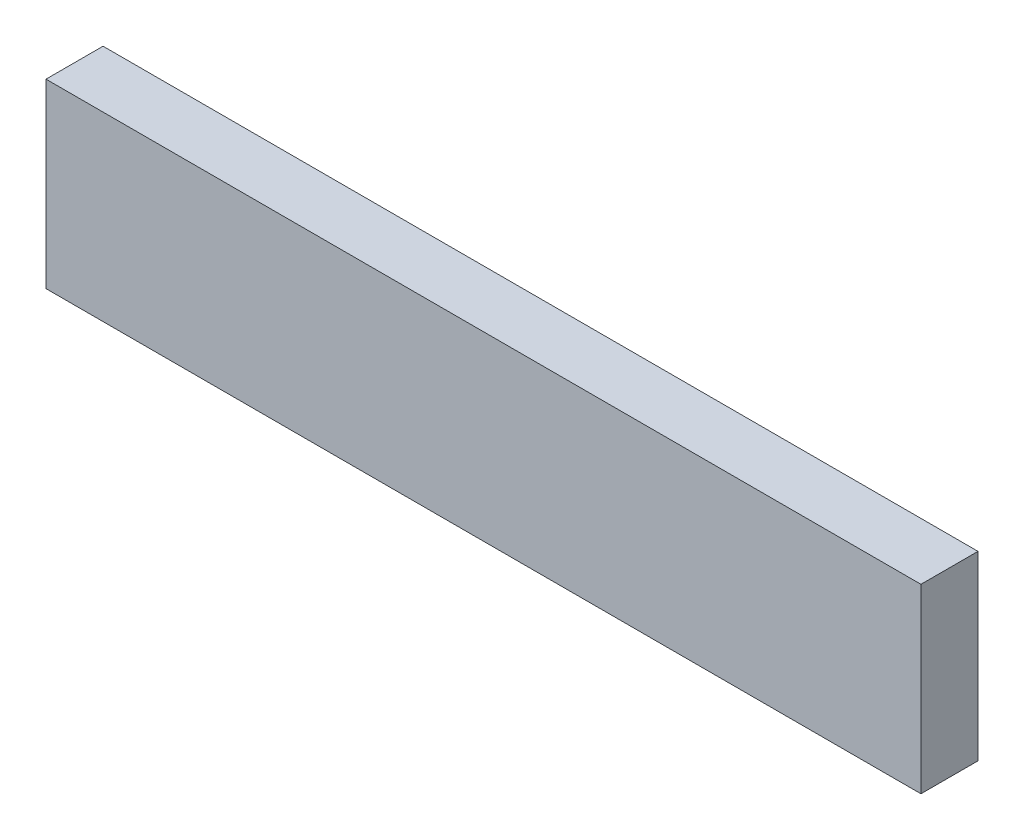
SolidWorks part; units mm, degrees
material "PE High Density"
ref_plane "Front Plane" through (0, 0, 0) normal (0, 0, 1) x (1, 0, 0)
ref_plane "Top Plane" through (0, 0, 0) normal (0, 1, 0) x (1, 0, 0)
ref_plane "Right Plane" through (0, 0, 0) normal (1, 0, 0) x (0, 0, -1)
sketch "Sketch1" plane through (0, 0, 0) normal (0, 0, 1) x (1, 0, 0)
  line L1 (-73.025, 15.1438) -> (73.025, 15.1438)
  line L2 (-73.025, 15.1438) -> (-73.025, -15.1438)
  line L3 (-73.025, -15.1438) -> (73.025, -15.1438)
  line L4 (73.025, 15.1438) -> (73.025, -15.1438)
  line L5 (-73.025, 15.1438) -> (73.025, -15.1438) construction
  line L6 (-73.025, -15.1438) -> (73.025, 15.1438) construction
  line L12 (-68.2625, 15.875) -> (-68.2625, -15.875) construction
  line L15 (-73.025, 0) -> (73.025, 0) construction
  line L16 (0, -15.1438) -> (0, 15.1438) construction
  point P0 (0, 0)
  dimension "D1" = 146.05
  dimension "D2" = 30.2876
  dimension "D9" = 4.7625
extrude "Boss-Extrude1" add sketch "Sketch1" along normal blind 9.525
sketch "Sketch2" plane through (73.025, 0, 0) normal (1, 0, 0) x (0, 0, -1)
  line L0 (-4.7625, 15.1438) -> (-4.7625, -15.1438) construction
  line L1 (-9.525, 15.1438) -> (0, 15.1438) construction
  line L2 (-9.525, -15.1438) -> (0, -15.1438) construction
  line L3 (-9.525, 0) -> (0, 0) construction
  line L4 (-9.525, -15.1438) -> (-9.525, 15.1438) construction
  circle A0 centre (-4.7625, 7.8438) radius 2.2479
  dimension "D1" = 4.4958
  dimension "D3" = 4.7625
  dimension "D2" = 7.3
equation "\"Plate Width\" = 3.5in"
equation "\"Plate Thickness\" = 0.375in"
equation "\"Num holes\" = 4"
equation "\"Plate Height\" = 1.25in"
equation "\"Top Plate Width\" = 4.5in"
equation "\"Plate Clearance Hole Diameter\" = 0.125in"
equation "\"Plate Tap Hole Diameter\" = 0.116in"
equation "\"Bottom Plate Length\" = 6.5in"
equation "\"Number Eight Clearance Size\" = 0.177in"
equation "\"D1@Sketch1\"=\"Bottom Plate Length\" - \"Plate Thickness\" * 2"
equation "\"D2@Sketch1\"=30.28757mm"
equation "\"D9@Sketch1\"=\"Plate Thickness\"/2"
equation "\"D1@Boss-Extrude1\"=\"Plate Thickness\""
equation "\"D1@Sketch2\"=\"Number Eight Clearance Size\""
equation "\"D1@Cut-Extrude1\"=0.8 - \"Plate Thickness\""
equation "\"Back Brace Height\" = 1.1962912in"
